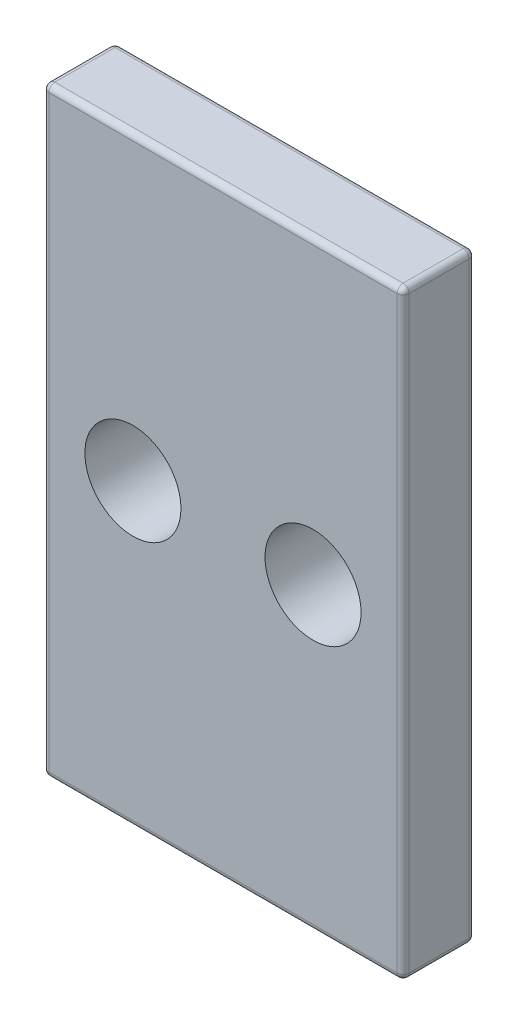
SolidWorks part; units mm, degrees
ref_plane "Płaszczyzna przednia" through (0, 0, 0) normal (0, 0, 1) x (1, 0, 0)
ref_plane "Płaszczyzna górna" through (0, 0, 0) normal (0, 1, 0) x (1, 0, 0)
ref_plane "Płaszczyzna prawa" through (0, 0, 0) normal (1, 0, 0) x (0, 0, -1)
sketch "Sketch1" plane through (0, 0, 0) normal (0, 0, 1) x (1, 0, 0)
  line L0 (0, 0) -> (26.9472, 0) construction
  line L1 (-15, 25) -> (15, 25)
  line L2 (-15, 25) -> (-15, -25)
  line L3 (-15, -25) -> (15, -25)
  line L4 (15, 25) -> (15, -25)
  line L5 (-15, 25) -> (15, -25) construction
  line L6 (-15, -25) -> (15, 25) construction
  line L7 (26.9472, 0) -> (-27.3648, 0) construction
  circle A0 centre (-7.5, 0) radius 4
  circle A1 centre (7.5, 0) radius 4
  point P0 (0, 0)
  dimension "D5" = 8
  dimension "D6" = 8
  dimension "D1" = 15
  dimension "D2" = 7.5
  dimension "D3" = 30
  dimension "D4" = 50
extrude "Boss-Extrude1" add sketch "Sketch1" along normal blind 6
fillet "Fillet1" radius 0.5 12 edges at (0, 25, 6) (0, 25, 0) (15, 0, 6) (15, 25, 3) (15, 0, 0) (0, -25, 6) (15, -25, 3) (0, -25, 0) (-15, 25, 3) (-15, 0, 6) (-15, -25, 3) (-15, 0, 0)
